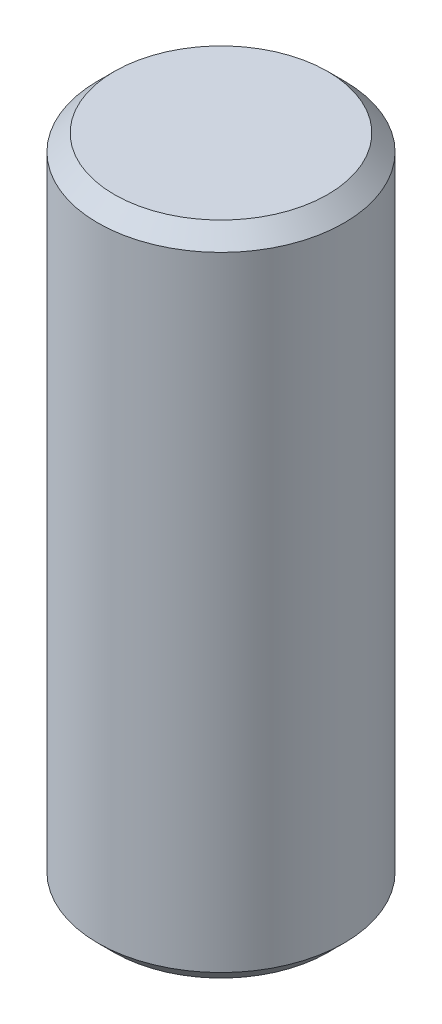
SolidWorks part; units mm, degrees
material "普通碳钢"
ref_plane "前视基准面" through (0, 0, 0) normal (0, 0, 1) x (1, 0, 0)
ref_plane "上视基准面" through (0, 0, 0) normal (0, 1, 0) x (1, 0, 0)
ref_plane "右视基准面" through (0, 0, 0) normal (1, 0, 0) x (0, 0, -1)
sketch "草图1" plane through (0, 0, 0) normal (0, 1, 0) x (1, 0, 0)
  circle A0 centre (0, 0) radius 1.5
  dimension "D1" = 3
extrude "凸台-拉伸1" add sketch "草图1" along normal blind 8
chamfer "倒角1" distance 0.2 angle 45 2 edges at (0, 8, 1.5) (0, 0, 1.5)
